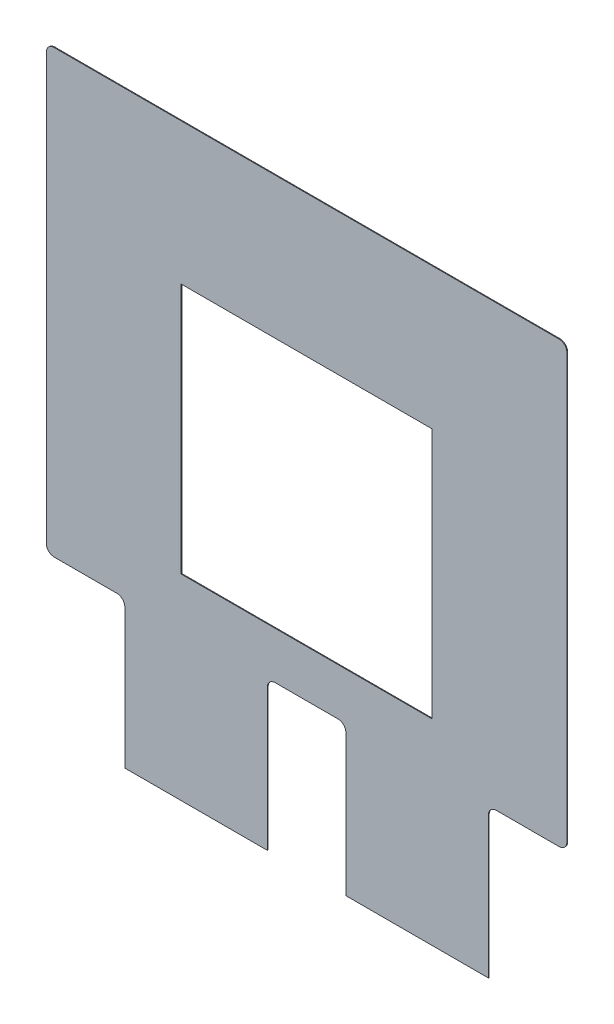
SolidWorks part; units mm, degrees
ref_plane "Alzado" through (0, 0, 0) normal (0, 0, 1) x (1, 0, 0)
ref_plane "Planta" through (0, 0, 0) normal (0, 1, 0) x (1, 0, 0)
ref_plane "Vista lateral" through (0, 0, 0) normal (1, 0, 0) x (0, 0, -1)
sketch "Model" plane through (0, 0, 0) normal (0, 0, 1) x (1, 0, 0)
  line L0 (31.5488, 11.0823) -> (31.5488, -20.9177)
  line L1 (16.0488, 11.0823) -> (31.5488, 11.0823)
  line L2 (-0.4512, 11.0823) -> (16.0488, 11.0823)
  line L3 (-0.4512, -20.9177) -> (-0.4512, 11.0823)
  line L4 (31.5488, -20.9177) -> (-0.4512, -20.9177)
  line L5 (34.7124, 29.0823) -> (47.7124, 29.0823)
  line L6 (48.7124, -25.9177) -> (48.7124, 28.0823)
  line L7 (39.7124, -26.9177) -> (47.7124, -26.9177)
  line L8 (38.7124, -45.9177) -> (38.7124, -27.9177)
  line L9 (20.5488, -27.9177) -> (20.5488, -45.9177)
  line L10 (11.5488, -26.9177) -> (19.5488, -26.9177)
  line L11 (10.5488, -45.9177) -> (10.5488, -27.9177)
  line L12 (-7.6148, -28.1394) -> (-7.6148, -45.9177)
  line L13 (-16.6148, -27.1394) -> (-8.6148, -27.1394)
  line L14 (-17.6148, 28.0823) -> (-17.6148, -26.1394)
  line L15 (-3.6148, 29.0823) -> (-16.6148, 29.0823)
  line L16 (-3.6148, 29.0823) -> (34.7124, 29.0823)
  line L17 (20.5488, -45.9177) -> (38.7124, -45.9177)
  line L18 (-7.6148, -45.9177) -> (10.5488, -45.9177)
  arc A0 (48.7124, 28.0823) -> (47.7124, 29.0823) centre (47.7124, 28.0823) ccw
  arc A1 (47.7124, -26.9177) -> (48.7124, -25.9177) centre (47.7124, -25.9177) ccw
  arc A2 (39.7124, -26.9177) -> (38.7124, -27.9177) centre (39.7124, -27.9177) ccw
  arc A3 (20.5488, -27.9177) -> (19.5488, -26.9177) centre (19.5488, -27.9177) ccw
  arc A4 (11.5488, -26.9177) -> (10.5488, -27.9177) centre (11.5488, -27.9177) ccw
  arc A5 (-7.6148, -28.1394) -> (-8.6148, -27.1394) centre (-8.6148, -28.1394) ccw
  arc A6 (-17.6148, -26.1394) -> (-16.6148, -27.1394) centre (-16.6148, -26.1394) ccw
  arc A7 (-16.6148, 29.0823) -> (-17.6148, 28.0823) centre (-16.6148, 28.0823) ccw
extrude "Saliente-Extruir1" add sketch "Model" along normal blind 0.1
